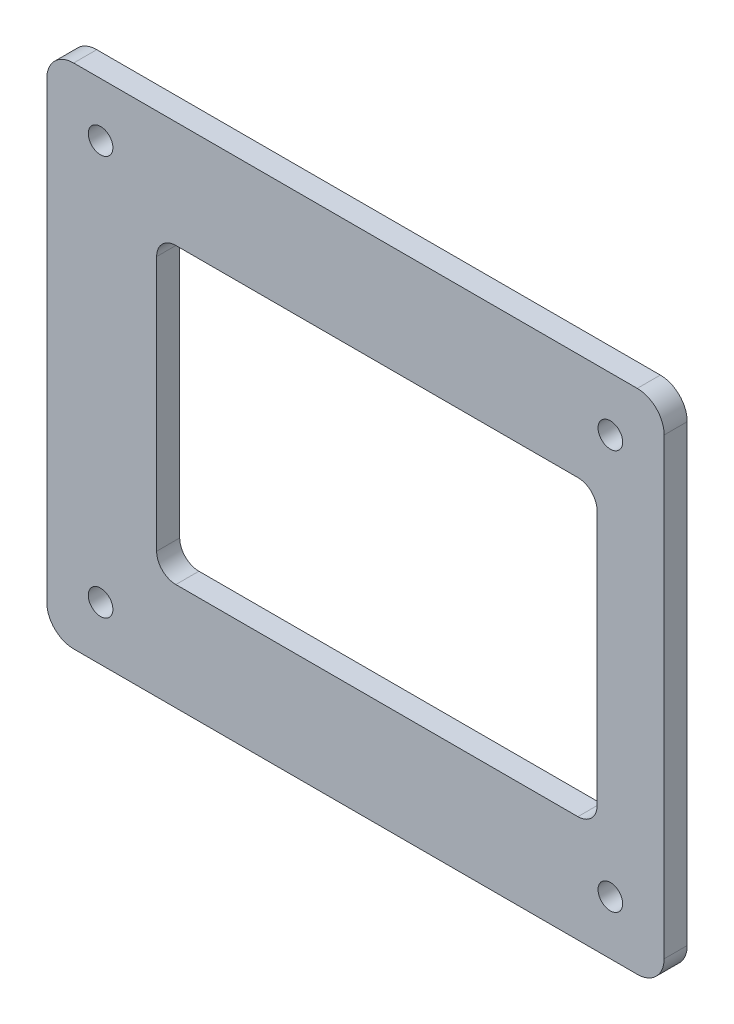
SolidWorks part; units mm, degrees
material "Acrylic (Medium-high impact)"
ref_plane "Front Plane" through (0, 0, 0) normal (0, 0, 1) x (1, 0, 0)
ref_plane "Top Plane" through (0, 0, 0) normal (0, 1, 0) x (1, 0, 0)
ref_plane "Right Plane" through (0, 0, 0) normal (1, 0, 0) x (0, 0, -1)
sketch "Sketch1" plane through (0, 0, 0) normal (0, 0, 1) x (1, 0, 0)
  line L1 (0, 0) -> (80.3, 0)
  line L2 (0, 0) -> (0, 66)
  line L3 (0, 66) -> (80.3, 66)
  line L4 (80.3, 0) -> (80.3, 66)
  dimension "D1" = 80.3
  dimension "D2" = 66
extrude "Boss-Extrude1" add sketch "Sketch1" along normal blind 3
hole_wizard "Ø3.2 (3.2) Diameter Hole1" positions "Sketch4" profile "Sketch3" hole size "Ø3.2" standard "ANSI Metric" end condition through all
sketch "Sketch4" plane through (0, 0, 3) normal (0, 0, 1) x (1, 0, 0)
  line L0 (80.3, 0) -> (80.3, 66) construction
  line L1 (80.3, 66) -> (0, 66) construction
  line L2 (0, 66) -> (0, 0) construction
  line L3 (0, 0) -> (80.3, 0) construction
  point P0 (7, 59)
  point P2 (73.3, 59)
  point P4 (73.3, 7)
  point P6 (7, 7)
  dimension "D1" = 7
  dimension "D2" = 7
  dimension "D3" = 7
  dimension "D4" = 7
sketch "Sketch3" plane through (7, 59, 3) normal (1, 0, 0) x (0, -1, 0)
  line L0 (0, 0) -> (0, 3)
  line L1 (0, 3) -> (1.6, 3)
  line L2 (1.6, 3) -> (1.6, 0)
  line L5 (1.6, 0) -> (0, 0)
  line L11 (0, -6.35) -> (0, 107.95) construction
  dimension "Thru Hole Dia." = 3.2
  dimension "Thru Hole Depth" = 3
sketch "Sketch2" plane through (0, 0, 3) normal (0, 0, 1) x (1, 0, 0)
  line L0 (0, 66) -> (0, 0) construction
  line L1 (14.29, 13.9) -> (71.58, 13.9)
  line L2 (14.29, 13.9) -> (14.29, 52.09)
  line L3 (14.29, 52.09) -> (71.58, 52.09)
  line L4 (71.58, 13.9) -> (71.58, 52.09)
  line L5 (0, 0) -> (80.3, 0) construction
  dimension "D1" = 57.29
  dimension "D2" = 38.19
  dimension "D3" = 14.29
  dimension "D4" = 13.9
extrude "Cut-Extrude1" cut sketch "Sketch2" against normal through all
fillet "Fillet1" radius 3.5 4 edges at (0, 0, 1.5) (80.3, 0, 1.5) (80.3, 66, 1.5) (0, 66, 1.5)
fillet "Fillet2" radius 2.5 4 edges at (14.29, 13.9, 1.5) (71.58, 13.9, 1.5) (71.58, 52.09, 1.5) (14.29, 52.09, 1.5)
